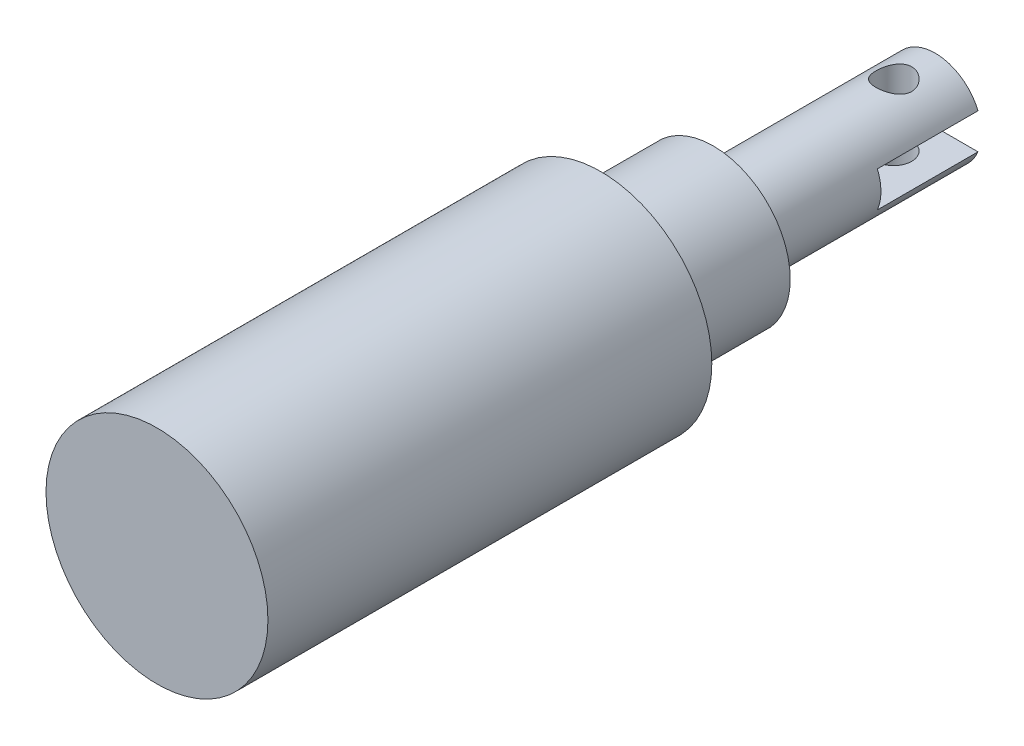
SolidWorks part; units mm, degrees
material "Cast Carbon Steel"
ref_plane "Front Plane" through (0, 0, 0) normal (0, 0, 1) x (1, 0, 0)
ref_plane "Top Plane" through (0, 0, 0) normal (0, 1, 0) x (1, 0, 0)
ref_plane "Right Plane" through (0, 0, 0) normal (1, 0, 0) x (0, 0, -1)
sketch "Sketch1" plane through (0, 0, 0) normal (0, 0, 1) x (1, 0, 0)
  circle A0 centre (0, 0) radius 9.525
extrude "Extrude1" add sketch "Sketch1" along normal blind 38.1
sketch "Sketch2" plane through (0, 0, 0) normal (0, 0, -1) x (-1, 0, 0)
  circle A0 centre (0, 0) radius 6.604
extrude "Extrude2" add sketch "Sketch2" along normal blind 9.652
sketch "Sketch3" plane through (0, 0, -9.652) normal (0, 0, -1) x (-1, 0, 0)
  circle A0 centre (0, 0) radius 3.9751
extrude "Extrude3" add sketch "Sketch3" along normal blind 19.05
sketch "Sketch4" plane through (0, 0, -28.702) normal (0, 0, -1) x (-1, 0, 0)
  line L1 (-5.016, 1.524) -> (5.144, 1.524)
  line L2 (-5.016, 1.524) -> (-5.016, -1.524)
  line L3 (-5.016, -1.524) -> (5.144, -1.524)
  line L4 (5.144, 1.524) -> (5.144, -1.524)
  dimension "D1" = 10.16
  dimension "D2" = 3.048
  dimension "D3" = 1.524
extrude "Cut-Extrude1" cut sketch "Sketch4" against normal blind 8.636
sketch "Sketch5" plane through (0, 0, 0) normal (0, 1, 0) x (1, 0, 0)
  line L0 (3.6714, 28.702) -> (-3.6714, 28.702) construction
  circle A0 centre (0, 25.146) radius 1.5367
  point P2 (0, 28.702)
  dimension "D1" = 3.556
extrude "Cut-Extrude2" cut sketch "Sketch5" against normal through all and the other way through all
